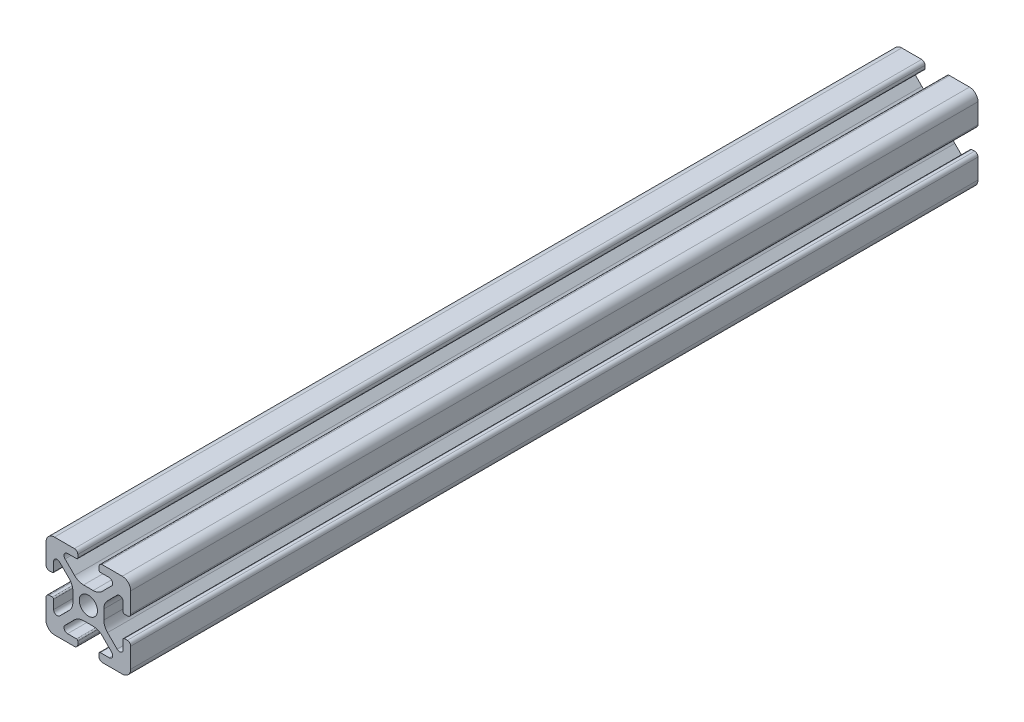
SolidWorks part; units mm, degrees
ref_plane "Front" through (0, 0, 0) normal (0, 0, 1) x (1, 0, 0)
ref_plane "Top" through (0, 0, 0) normal (0, 1, 0) x (1, 0, 0)
ref_plane "Right" through (0, 0, 0) normal (1, 0, 0) x (0, 0, -1)
sketch "Support-Front" plane through (0, 0, 0) normal (0, 0, 1) x (1, 0, 0)
  line L0 (10, 0) -> (-10, 0) construction
  line L1 (-10, -10) -> (10, -10)
  line L2 (-10, -10) -> (-10, 10)
  line L3 (-10, 10) -> (10, 10)
  line L4 (10, -10) -> (10, 10)
  line L5 (0, 10) -> (0, -10) construction
  dimension "Height-Profile" = 20
  dimension "Width-Profile" = 20
sketch "Support-Right-Length" plane through (0, 0, 0) normal (1, 0, 0) x (0, 0, -1)
  line L0 (0, -10) -> (0, 10) construction
  line L1 (-25, 10) -> (25, 10)
  line L2 (-25, 10) -> (-25, -10)
  line L3 (-25, -10) -> (25, -10)
  line L4 (25, 10) -> (25, -10)
  dimension "Length-Profile" = 50
sketch "Support-Profile" plane through (0, 0, 0) normal (0, 0, 1) x (1, 0, 0)
  line L8 (4.9176, -8.2) -> (2.8, -8.2)
  line L9 (2.5, -8.5) -> (2.5, -9.2)
  line L10 (3.3, -10) -> (8, -10)
  line L11 (10, -8) -> (10, -3.3)
  line L24 (9.2, -2.5) -> (8.5, -2.5)
  line L25 (8.2, -2.8) -> (8.2, -4.9176)
  line L26 (6.779, -5.5062) -> (4.5287, -3.2559)
  line L27 (3.65, -1.1346) -> (3.65, 1.1346)
  line L28 (4.5287, 3.2559) -> (6.779, 5.5062)
  line L29 (8.2, 4.9176) -> (8.2, 2.8)
  line L30 (8.5, 2.5) -> (9.2, 2.5)
  line L31 (10, 3.3) -> (10, 8)
  line L32 (8, 10) -> (3.3, 10)
  line L33 (2.5, 9.2) -> (2.5, 8.5)
  line L34 (2.8, 8.2) -> (4.9176, 8.2)
  line L35 (5.5062, 6.779) -> (3.2559, 4.5287)
  line L40 (1.1346, 3.65) -> (-1.1346, 3.65)
  line L41 (-3.2559, 4.5287) -> (-5.5062, 6.779)
  line L42 (-4.9176, 8.2) -> (-2.8, 8.2)
  line L43 (-2.5, 8.5) -> (-2.5, 9.2)
  line L44 (-3.3, 10) -> (-8, 10)
  line L45 (-10, 8) -> (-10, 3.3)
  line L46 (-9.2, 2.5) -> (-8.5, 2.5)
  line L47 (-8.2, 2.8) -> (-8.2, 4.9176)
  line L48 (-6.779, 5.5062) -> (-4.5287, 3.2559)
  line L49 (-3.65, 1.1346) -> (-3.65, -1.1346)
  line L50 (-4.5287, -3.2559) -> (-6.779, -5.5062)
  line L51 (-8.2, -4.9176) -> (-8.2, -2.8)
  line L52 (-8.5, -2.5) -> (-9.2, -2.5)
  line L53 (-10, -3.3) -> (-10, -8)
  line L54 (-8, -10) -> (-3.3, -10)
  line L55 (-2.5, -9.2) -> (-2.5, -8.5)
  line L56 (-2.8, -8.2) -> (-4.9176, -8.2)
  line L57 (-5.5062, -6.779) -> (-3.2559, -4.5287)
  line L58 (-1.1346, -3.65) -> (1.1346, -3.65)
  line L59 (3.2559, -4.5287) -> (5.5062, -6.779)
  circle A2 centre (0, 0) radius 2.15
  arc A3 (2.8, -8.2) -> (2.5, -8.5) centre (2.8, -8.5) ccw
  arc A5 (2.5, -9.2) -> (3.3, -10) centre (3.3, -9.2) ccw
  arc A24 (8, -10) -> (10, -8) centre (8, -8) ccw
  arc A25 (10, -3.3) -> (9.2, -2.5) centre (9.2, -3.3) ccw
  arc A26 (8.5, -2.5) -> (8.2, -2.8) centre (8.5, -2.8) ccw
  arc A27 (6.779, -5.5062) -> (8.2, -4.9176) centre (7.3676, -4.9176) ccw
  arc A28 (3.65, -1.1346) -> (4.5287, -3.2559) centre (6.65, -1.1346) ccw
  arc A29 (4.5287, 3.2559) -> (3.65, 1.1346) centre (6.65, 1.1346) ccw
  arc A30 (8.2, 4.9176) -> (6.779, 5.5062) centre (7.3676, 4.9176) ccw
  arc A31 (8.2, 2.8) -> (8.5, 2.5) centre (8.5, 2.8) ccw
  arc A32 (9.2, 2.5) -> (10, 3.3) centre (9.2, 3.3) ccw
  arc A33 (10, 8) -> (8, 10) centre (8, 8) ccw
  arc A34 (3.3, 10) -> (2.5, 9.2) centre (3.3, 9.2) ccw
  arc A35 (2.5, 8.5) -> (2.8, 8.2) centre (2.8, 8.5) ccw
  arc A38 (5.5062, 6.779) -> (4.9176, 8.2) centre (4.9176, 7.3676) ccw
  arc A39 (1.1346, 3.65) -> (3.2559, 4.5287) centre (1.1346, 6.65) ccw
  arc A44 (-3.2559, 4.5287) -> (-1.1346, 3.65) centre (-1.1346, 6.65) ccw
  arc A45 (-4.9176, 8.2) -> (-5.5062, 6.779) centre (-4.9176, 7.3676) ccw
  arc A46 (-2.8, 8.2) -> (-2.5, 8.5) centre (-2.8, 8.5) ccw
  arc A47 (-2.5, 9.2) -> (-3.3, 10) centre (-3.3, 9.2) ccw
  arc A48 (-8, 10) -> (-10, 8) centre (-8, 8) ccw
  arc A49 (-10, 3.3) -> (-9.2, 2.5) centre (-9.2, 3.3) ccw
  arc A50 (-8.5, 2.5) -> (-8.2, 2.8) centre (-8.5, 2.8) ccw
  arc A51 (-6.779, 5.5062) -> (-8.2, 4.9176) centre (-7.3676, 4.9176) ccw
  arc A52 (-3.65, 1.1346) -> (-4.5287, 3.2559) centre (-6.65, 1.1346) ccw
  arc A53 (-4.5287, -3.2559) -> (-3.65, -1.1346) centre (-6.65, -1.1346) ccw
  arc A54 (-8.2, -4.9176) -> (-6.779, -5.5062) centre (-7.3676, -4.9176) ccw
  arc A55 (-8.2, -2.8) -> (-8.5, -2.5) centre (-8.5, -2.8) ccw
  arc A56 (-9.2, -2.5) -> (-10, -3.3) centre (-9.2, -3.3) ccw
  arc A57 (-10, -8) -> (-8, -10) centre (-8, -8) ccw
  arc A58 (-3.3, -10) -> (-2.5, -9.2) centre (-3.3, -9.2) ccw
  arc A59 (-2.5, -8.5) -> (-2.8, -8.2) centre (-2.8, -8.5) ccw
  arc A60 (-5.5062, -6.779) -> (-4.9176, -8.2) centre (-4.9176, -7.3676) ccw
  arc A61 (-1.1346, -3.65) -> (-3.2559, -4.5287) centre (-1.1346, -6.65) ccw
  arc A62 (3.2559, -4.5287) -> (1.1346, -3.65) centre (1.1346, -6.65) ccw
  arc A63 (4.9176, -8.2) -> (5.5062, -6.779) centre (4.9176, -7.3676) ccw
ref_plane "Ref-Plane-1" through (0, 0, 25) normal (0, 0, 1) x (1, 0, 0)
ref_plane "Ref-Plane-2" through (0, 0, -25) normal (0, 0, 1) x (1, 0, 0)
sketch "Sketch4" plane through (0, 0, 25) normal (0, 0, 1) x (1, 0, 0)
  line L0 (-10, -10) -> (-10, 10) construction
  line L1 (-10, -10) -> (10, -10) construction
  line L2 (10, -10) -> (10, 10) construction
  line L3 (-10, 10) -> (10, 10) construction
  line L4 (-10, -10) -> (-10, 10)
  line L5 (-10, -10) -> (10, -10)
  line L6 (10, -10) -> (10, 10)
  line L7 (-10, 10) -> (10, 10)
extrude "Body" add sketch "Sketch4" against normal blind 200
sketch "Sketch16" plane through (0, 0, 0) normal (0, 0, 1) x (1, 0, 0)
  line L40 (4.9176, -8.2) -> (2.8, -8.2)
  line L41 (2.5, -8.5) -> (2.5, -9.2)
  line L42 (3.3, -10) -> (8, -10)
  line L43 (10, -8) -> (10, -3.3)
  line L44 (9.2, -2.5) -> (8.5, -2.5)
  line L45 (8.2, -2.8) -> (8.2, -4.9176)
  line L46 (6.779, -5.5062) -> (4.5287, -3.2559)
  line L47 (3.65, -1.1346) -> (3.65, 1.1346)
  line L48 (4.5287, 3.2559) -> (6.779, 5.5062)
  line L49 (8.2, 4.9176) -> (8.2, 2.8)
  line L50 (8.5, 2.5) -> (9.2, 2.5)
  line L51 (10, 3.3) -> (10, 8)
  line L52 (8, 10) -> (3.3, 10)
  line L53 (2.5, 9.2) -> (2.5, 8.5)
  line L54 (2.8, 8.2) -> (4.9176, 8.2)
  line L55 (5.5062, 6.779) -> (3.2559, 4.5287)
  line L56 (1.1346, 3.65) -> (-1.1346, 3.65)
  line L57 (-3.2559, 4.5287) -> (-5.5062, 6.779)
  line L58 (-4.9176, 8.2) -> (-2.8, 8.2)
  line L59 (-2.5, 8.5) -> (-2.5, 9.2)
  line L60 (-3.3, 10) -> (-8, 10)
  line L61 (-10, 8) -> (-10, 3.3)
  line L62 (-9.2, 2.5) -> (-8.5, 2.5)
  line L63 (-8.2, 2.8) -> (-8.2, 4.9176)
  line L64 (-6.779, 5.5062) -> (-4.5287, 3.2559)
  line L65 (-3.65, 1.1346) -> (-3.65, -1.1346)
  line L66 (-4.5287, -3.2559) -> (-6.779, -5.5062)
  line L67 (-8.2, -4.9176) -> (-8.2, -2.8)
  line L68 (-8.5, -2.5) -> (-9.2, -2.5)
  line L69 (-10, -3.3) -> (-10, -8)
  line L70 (-8, -10) -> (-3.3, -10)
  line L71 (-2.5, -9.2) -> (-2.5, -8.5)
  line L72 (-2.8, -8.2) -> (-4.9176, -8.2)
  line L73 (-5.5062, -6.779) -> (-3.2559, -4.5287)
  line L74 (-1.1346, -3.65) -> (1.1346, -3.65)
  line L75 (3.2559, -4.5287) -> (5.5062, -6.779)
  line L76 (4.9176, -8.2) -> (2.8, -8.2)
  line L77 (2.5, -8.5) -> (2.5, -9.2)
  line L78 (3.3, -10) -> (8, -10)
  line L79 (10, -8) -> (10, -3.3)
  line L80 (9.2, -2.5) -> (8.5, -2.5)
  line L81 (8.2, -2.8) -> (8.2, -4.9176)
  line L82 (6.779, -5.5062) -> (4.5287, -3.2559)
  line L83 (3.65, -1.1346) -> (3.65, 1.1346)
  line L84 (4.5287, 3.2559) -> (6.779, 5.5062)
  line L85 (8.2, 4.9176) -> (8.2, 2.8)
  line L86 (8.5, 2.5) -> (9.2, 2.5)
  line L87 (10, 3.3) -> (10, 8)
  line L88 (8, 10) -> (3.3, 10)
  line L89 (2.5, 9.2) -> (2.5, 8.5)
  line L90 (2.8, 8.2) -> (4.9176, 8.2)
  line L91 (5.5062, 6.779) -> (3.2559, 4.5287)
  line L92 (1.1346, 3.65) -> (-1.1346, 3.65)
  line L93 (-3.2559, 4.5287) -> (-5.5062, 6.779)
  line L94 (-4.9176, 8.2) -> (-2.8, 8.2)
  line L95 (-2.5, 8.5) -> (-2.5, 9.2)
  line L96 (-3.3, 10) -> (-8, 10)
  line L97 (-10, 8) -> (-10, 3.3)
  line L98 (-9.2, 2.5) -> (-8.5, 2.5)
  line L99 (-8.2, 2.8) -> (-8.2, 4.9176)
  line L100 (-6.779, 5.5062) -> (-4.5287, 3.2559)
  line L101 (-3.65, 1.1346) -> (-3.65, -1.1346)
  line L102 (-4.5287, -3.2559) -> (-6.779, -5.5062)
  line L103 (-8.2, -4.9176) -> (-8.2, -2.8)
  line L104 (-8.5, -2.5) -> (-9.2, -2.5)
  line L105 (-10, -3.3) -> (-10, -8)
  line L106 (-8, -10) -> (-3.3, -10)
  line L107 (-2.5, -9.2) -> (-2.5, -8.5)
  line L108 (-2.8, -8.2) -> (-4.9176, -8.2)
  line L109 (-5.5062, -6.779) -> (-3.2559, -4.5287)
  line L110 (-1.1346, -3.65) -> (1.1346, -3.65)
  line L111 (3.2559, -4.5287) -> (5.5062, -6.779)
  circle A7 centre (0, 0) radius 2.15 construction
  circle A8 centre (0, 0) radius 2.15
  arc A43 (2.8, -8.2) -> (2.5, -8.5) centre (2.8, -8.5) ccw
  arc A44 (2.5, -9.2) -> (3.3, -10) centre (3.3, -9.2) ccw
  arc A45 (8, -10) -> (10, -8) centre (8, -8) ccw
  arc A46 (10, -3.3) -> (9.2, -2.5) centre (9.2, -3.3) ccw
  arc A47 (8.5, -2.5) -> (8.2, -2.8) centre (8.5, -2.8) ccw
  arc A48 (6.779, -5.5062) -> (8.2, -4.9176) centre (7.3676, -4.9176) ccw
  arc A49 (3.65, -1.1346) -> (4.5287, -3.2559) centre (6.65, -1.1346) ccw
  arc A50 (4.5287, 3.2559) -> (3.65, 1.1346) centre (6.65, 1.1346) ccw
  arc A51 (8.2, 4.9176) -> (6.779, 5.5062) centre (7.3676, 4.9176) ccw
  arc A52 (8.2, 2.8) -> (8.5, 2.5) centre (8.5, 2.8) ccw
  arc A53 (9.2, 2.5) -> (10, 3.3) centre (9.2, 3.3) ccw
  arc A54 (10, 8) -> (8, 10) centre (8, 8) ccw
  arc A55 (3.3, 10) -> (2.5, 9.2) centre (3.3, 9.2) ccw
  arc A56 (2.5, 8.5) -> (2.8, 8.2) centre (2.8, 8.5) ccw
  arc A57 (5.5062, 6.779) -> (4.9176, 8.2) centre (4.9176, 7.3676) ccw
  arc A58 (1.1346, 3.65) -> (3.2559, 4.5287) centre (1.1346, 6.65) ccw
  arc A59 (-3.2559, 4.5287) -> (-1.1346, 3.65) centre (-1.1346, 6.65) ccw
  arc A60 (-4.9176, 8.2) -> (-5.5062, 6.779) centre (-4.9176, 7.3676) ccw
  arc A61 (-2.8, 8.2) -> (-2.5, 8.5) centre (-2.8, 8.5) ccw
  arc A62 (-2.5, 9.2) -> (-3.3, 10) centre (-3.3, 9.2) ccw
  arc A63 (-8, 10) -> (-10, 8) centre (-8, 8) ccw
  arc A64 (-10, 3.3) -> (-9.2, 2.5) centre (-9.2, 3.3) ccw
  arc A65 (-8.5, 2.5) -> (-8.2, 2.8) centre (-8.5, 2.8) ccw
  arc A66 (-6.779, 5.5062) -> (-8.2, 4.9176) centre (-7.3676, 4.9176) ccw
  arc A67 (-3.65, 1.1346) -> (-4.5287, 3.2559) centre (-6.65, 1.1346) ccw
  arc A68 (-4.5287, -3.2559) -> (-3.65, -1.1346) centre (-6.65, -1.1346) ccw
  arc A69 (-8.2, -4.9176) -> (-6.779, -5.5062) centre (-7.3676, -4.9176) ccw
  arc A70 (-8.2, -2.8) -> (-8.5, -2.5) centre (-8.5, -2.8) ccw
  arc A71 (-9.2, -2.5) -> (-10, -3.3) centre (-9.2, -3.3) ccw
  arc A72 (-10, -8) -> (-8, -10) centre (-8, -8) ccw
  arc A73 (-3.3, -10) -> (-2.5, -9.2) centre (-3.3, -9.2) ccw
  arc A74 (-2.5, -8.5) -> (-2.8, -8.2) centre (-2.8, -8.5) ccw
  arc A75 (-5.5062, -6.779) -> (-4.9176, -8.2) centre (-4.9176, -7.3676) ccw
  arc A76 (-1.1346, -3.65) -> (-3.2559, -4.5287) centre (-1.1346, -6.65) ccw
  arc A77 (3.2559, -4.5287) -> (1.1346, -3.65) centre (1.1346, -6.65) ccw
  arc A78 (4.9176, -8.2) -> (5.5062, -6.779) centre (4.9176, -7.3676) ccw
  arc A79 (2.8, -8.2) -> (2.5, -8.5) centre (2.8, -8.5) ccw
  arc A80 (2.5, -9.2) -> (3.3, -10) centre (3.3, -9.2) ccw
  arc A81 (8, -10) -> (10, -8) centre (8, -8) ccw
  arc A82 (10, -3.3) -> (9.2, -2.5) centre (9.2, -3.3) ccw
  arc A83 (8.5, -2.5) -> (8.2, -2.8) centre (8.5, -2.8) ccw
  arc A84 (6.779, -5.5062) -> (8.2, -4.9176) centre (7.3676, -4.9176) ccw
  arc A85 (3.65, -1.1346) -> (4.5287, -3.2559) centre (6.65, -1.1346) ccw
  arc A86 (4.5287, 3.2559) -> (3.65, 1.1346) centre (6.65, 1.1346) ccw
  arc A87 (8.2, 4.9176) -> (6.779, 5.5062) centre (7.3676, 4.9176) ccw
  arc A88 (8.2, 2.8) -> (8.5, 2.5) centre (8.5, 2.8) ccw
  arc A89 (9.2, 2.5) -> (10, 3.3) centre (9.2, 3.3) ccw
  arc A90 (10, 8) -> (8, 10) centre (8, 8) ccw
  arc A91 (3.3, 10) -> (2.5, 9.2) centre (3.3, 9.2) ccw
  arc A92 (2.5, 8.5) -> (2.8, 8.2) centre (2.8, 8.5) ccw
  arc A93 (5.5062, 6.779) -> (4.9176, 8.2) centre (4.9176, 7.3676) ccw
  arc A94 (1.1346, 3.65) -> (3.2559, 4.5287) centre (1.1346, 6.65) ccw
  arc A95 (-3.2559, 4.5287) -> (-1.1346, 3.65) centre (-1.1346, 6.65) ccw
  arc A96 (-4.9176, 8.2) -> (-5.5062, 6.779) centre (-4.9176, 7.3676) ccw
  arc A97 (-2.8, 8.2) -> (-2.5, 8.5) centre (-2.8, 8.5) ccw
  arc A98 (-2.5, 9.2) -> (-3.3, 10) centre (-3.3, 9.2) ccw
  arc A99 (-8, 10) -> (-10, 8) centre (-8, 8) ccw
  arc A100 (-10, 3.3) -> (-9.2, 2.5) centre (-9.2, 3.3) ccw
  arc A101 (-8.5, 2.5) -> (-8.2, 2.8) centre (-8.5, 2.8) ccw
  arc A102 (-6.779, 5.5062) -> (-8.2, 4.9176) centre (-7.3676, 4.9176) ccw
  arc A103 (-3.65, 1.1346) -> (-4.5287, 3.2559) centre (-6.65, 1.1346) ccw
  arc A104 (-4.5287, -3.2559) -> (-3.65, -1.1346) centre (-6.65, -1.1346) ccw
  arc A105 (-8.2, -4.9176) -> (-6.779, -5.5062) centre (-7.3676, -4.9176) ccw
  arc A106 (-8.2, -2.8) -> (-8.5, -2.5) centre (-8.5, -2.8) ccw
  arc A107 (-9.2, -2.5) -> (-10, -3.3) centre (-9.2, -3.3) ccw
  arc A108 (-10, -8) -> (-8, -10) centre (-8, -8) ccw
  arc A109 (-3.3, -10) -> (-2.5, -9.2) centre (-3.3, -9.2) ccw
  arc A110 (-2.5, -8.5) -> (-2.8, -8.2) centre (-2.8, -8.5) ccw
  arc A111 (-5.5062, -6.779) -> (-4.9176, -8.2) centre (-4.9176, -7.3676) ccw
  arc A112 (-1.1346, -3.65) -> (-3.2559, -4.5287) centre (-1.1346, -6.65) ccw
  arc A113 (3.2559, -4.5287) -> (1.1346, -3.65) centre (1.1346, -6.65) ccw
  arc A114 (4.9176, -8.2) -> (5.5062, -6.779) centre (4.9176, -7.3676) ccw
  dimension "D1" = 0
extrude "Cut-Profile" cut sketch "Sketch16" against normal through all and the other way through all flip side to cut
